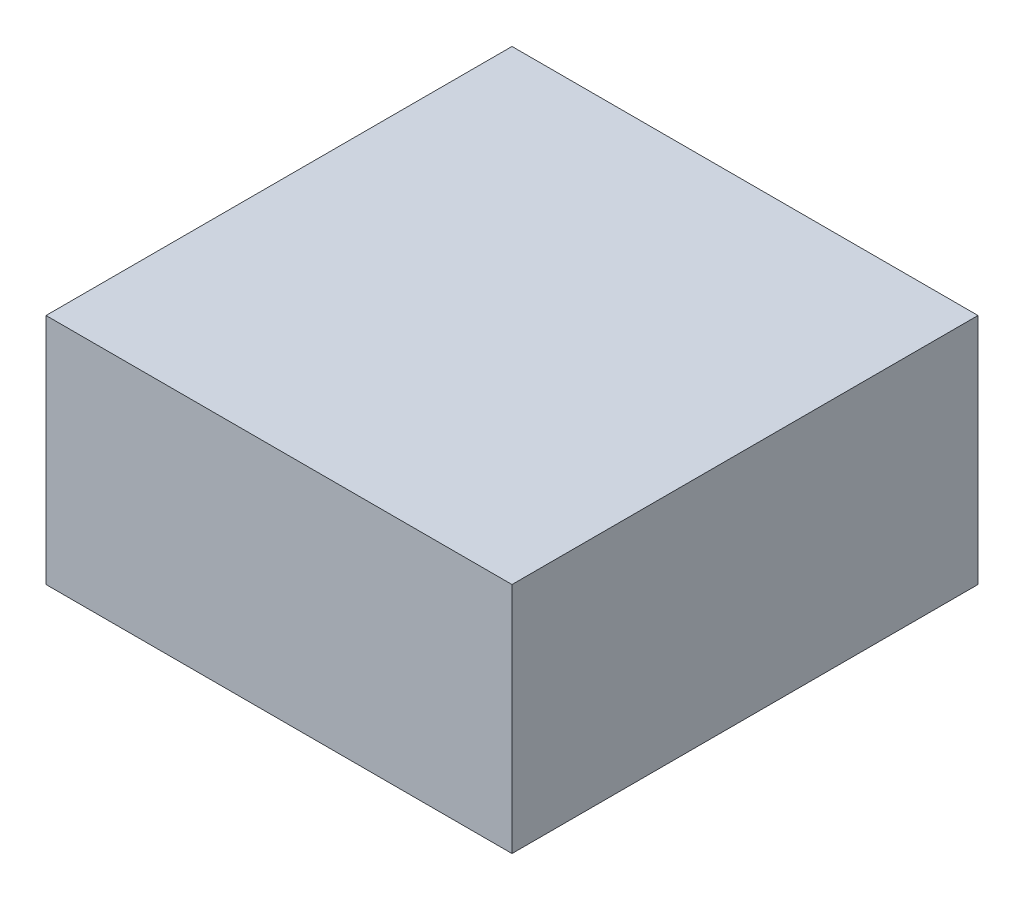
SolidWorks part; units mm, degrees
ref_plane "Front Plane" through (0, 0, 0) normal (0, 0, 1) x (1, 0, 0)
ref_plane "Top Plane" through (0, 0, 0) normal (0, 1, 0) x (1, 0, 0)
ref_plane "Right Plane" through (0, 0, 0) normal (1, 0, 0) x (0, 0, -1)
sketch "Sketch1" plane through (0, 0, 0) normal (0, 1, 0) x (1, 0, 0)
  line L1 (0, 0) -> (10, 0)
  line L2 (0, 0) -> (0, 10)
  line L3 (0, 10) -> (10, 10)
  line L4 (10, 0) -> (10, 10)
  dimension "D1" = 10
  dimension "D2" = 10
extrude "Boss-Extrude1" add sketch "Sketch1" along normal blind 5
